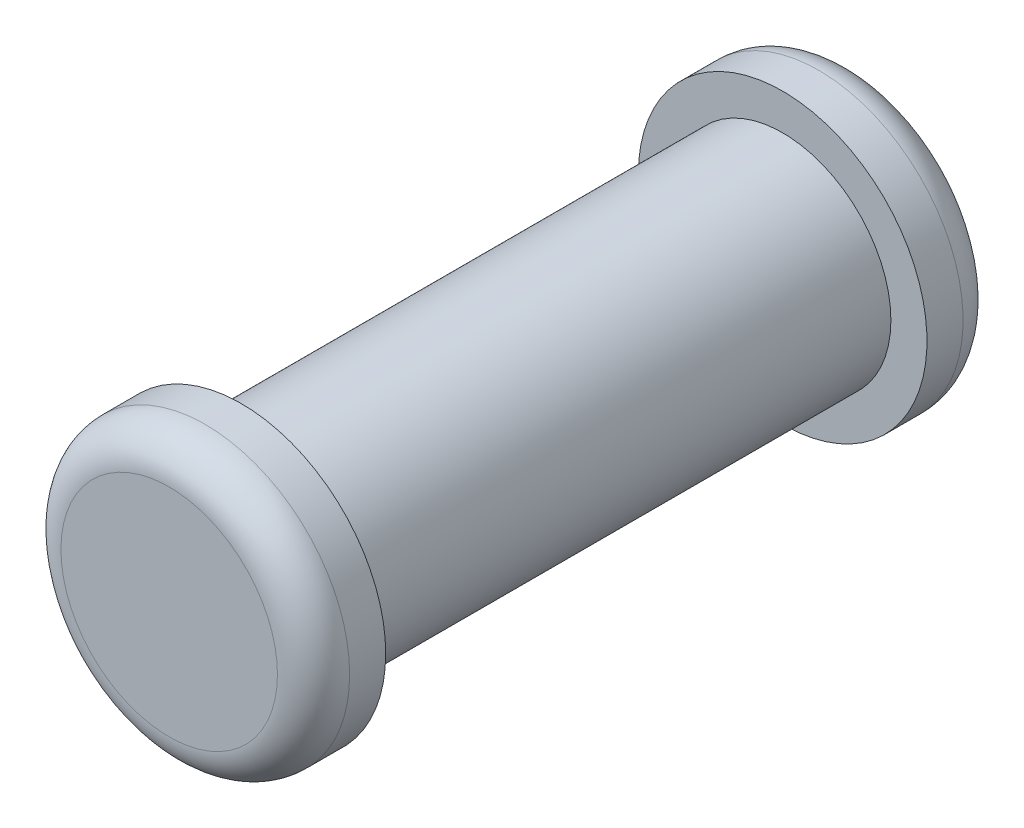
SolidWorks part; units mm, degrees
ref_plane "Front Plane" through (0, 0, 0) normal (0, 0, 1) x (1, 0, 0)
ref_plane "Top Plane" through (0, 0, 0) normal (0, 1, 0) x (1, 0, 0)
ref_plane "Right Plane" through (0, 0, 0) normal (1, 0, 0) x (0, 0, -1)
sketch "Sketch1" plane through (0, 0, 0) normal (0, 0, 1) x (1, 0, 0)
  circle A0 centre (0, 0) radius 1.5
  dimension "D1" = 3
extrude "Boss-Extrude1" add sketch "Sketch1" along normal blind 7.5
sketch "Sketch2" plane through (0, 0, 0) normal (0, 0, -1) x (-1, 0, 0)
  circle A0 centre (0, 0) radius 2
  dimension "D1" = 4
extrude "Boss-Extrude2" add sketch "Sketch2" along normal blind 1
sketch "Sketch3" plane through (0, 0, 7.5) normal (0, 0, 1) x (1, 0, 0)
  circle A1 centre (0, 0) radius 2
  circle A2 centre (0, 0) radius 2
  dimension "D1" = 0
extrude "Boss-Extrude3" add sketch "Sketch3" along normal blind 1
fillet "Fillet1" radius 0.5 2 edges at (-2, 0, -1) (2, 0, 8.5)
